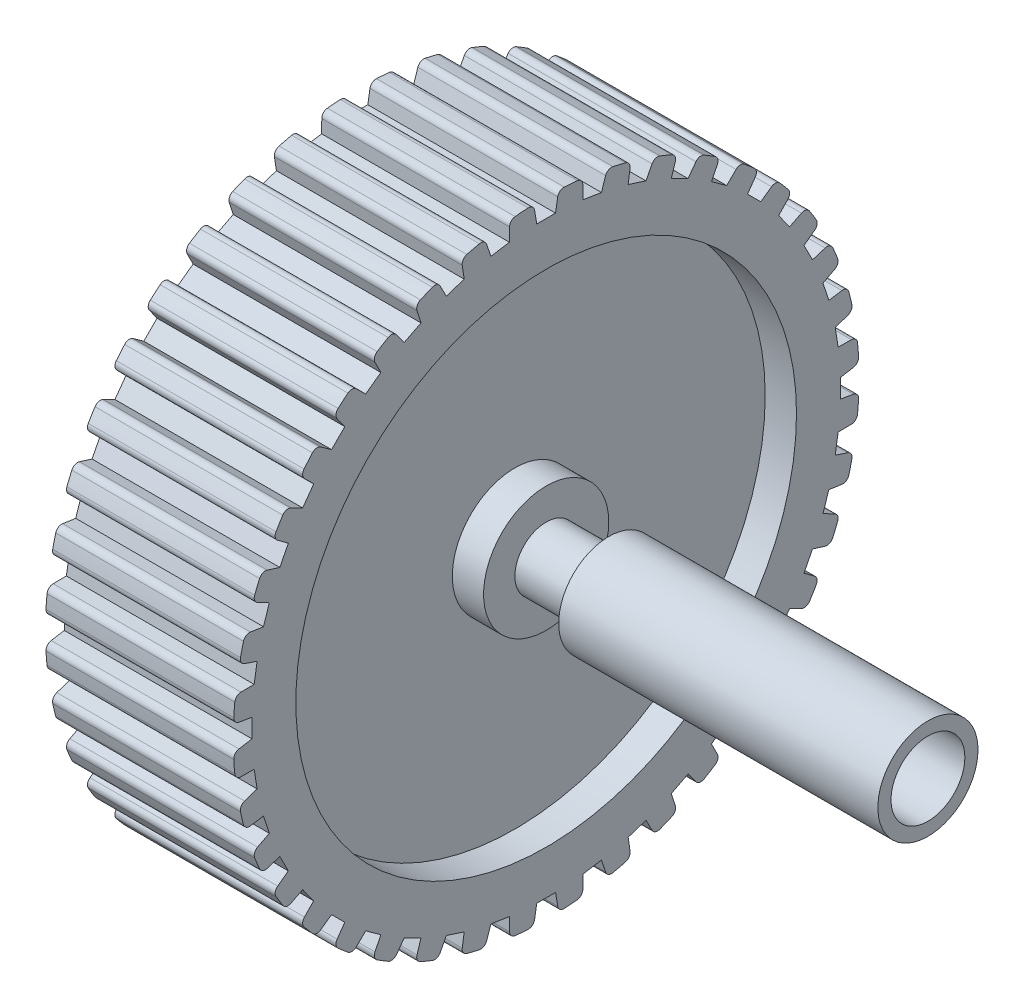
SolidWorks part; units mm, degrees
ref_plane "Front Plane" through (0, 0, 0) normal (0, 0, 1) x (1, 0, 0)
ref_plane "Top Plane" through (0, 0, 0) normal (0, 1, 0) x (1, 0, 0)
ref_plane "Right Plane" through (0, 0, 0) normal (1, 0, 0) x (0, 0, -1)
sketch "Sketch1" plane through (0, 0, 0) normal (0, 0, 1) x (1, 0, 0)
  line L0 (0, 0) -> (-52.2034, 0) construction
  line L1 (0, 5) -> (-30, 5)
  line L2 (-30, 5) -> (-30, 10)
  line L3 (-30, 10) -> (-25, 10)
  line L4 (-25, 10) -> (-25, 40)
  line L5 (-25, 40) -> (-30, 40)
  line L6 (-30, 40) -> (-30, 50)
  line L7 (-30, 50) -> (0, 50)
  line L8 (0, 50) -> (0, 40)
  line L9 (0, 40) -> (-5, 40)
  line L10 (-5, 40) -> (-5, 10)
  line L11 (-5, 10) -> (0, 10)
  line L12 (0, 10) -> (0, 5)
  dimension "D1" = 10
  dimension "D2" = 100
  dimension "D3" = 30
  dimension "D4" = 20
  dimension "D5" = 5
  dimension "D6" = 10
revolve "Revolve1" add sketch "Sketch1" angle 360 about L0
sketch "Sketch2" plane through (0, 0, 0) normal (1, 0, 0) x (0, 0, -1)
  line L0 (-2.5, 53) -> (-1.5, 47)
  line L1 (-1.5, 47) -> (1.5, 47)
  line L2 (1.5, 47) -> (2.5, 53)
  line L3 (2.5, 53) -> (-2.5, 53)
  circle A0 centre (0, 0) radius 50 construction
  point P3 (0, 47)
  point P6 (0, 53)
  point P7 (0, 50)
  dimension "D1" = 3
  dimension "D2" = 5
  dimension "D3" = 6
  dimension "D4" = 3
extrude "Cut-Extrude1" cut sketch "Sketch2" against normal blind 44
fillet "Fillet1" radius 1 2 edges at (-15, 49.9602, 1.9934) (-15, 49.9602, -1.9934)
pattern_circular "CirPattern1" count 40 over 360 about axis through (0, 0, 0) along (1, 0, 0) of "Cut-Extrude1", "Fillet1"
scale "Scale1" bodies to scale 103 scale about centroid uniform scaling yes scale factor 0.5
sketch "Sketch3" plane through (-22.5, 0, 0) normal (-1, 0, 0) x (0, 0, 1)
  circle A0 centre (0, 0) radius 2.5
extrude "Boss-Extrude1" add sketch "Sketch3" against normal blind 30
sketch "Sketch4" plane through (7.5, 0, 0) normal (1, 0, 0) x (0, 0, -1)
  circle A0 centre (0, 0) radius 4
extrude "Boss-Extrude2" add sketch "Sketch4" along normal blind 15.5 and the other way blind 10
sketch "Sketch5" plane through (23, 0, 0) normal (1, 0, 0) x (0, 0, -1)
  circle A0 centre (0, 0) radius 2.95
extrude "Cut-Extrude2" cut sketch "Sketch5" against normal blind 15.5 contours A0
